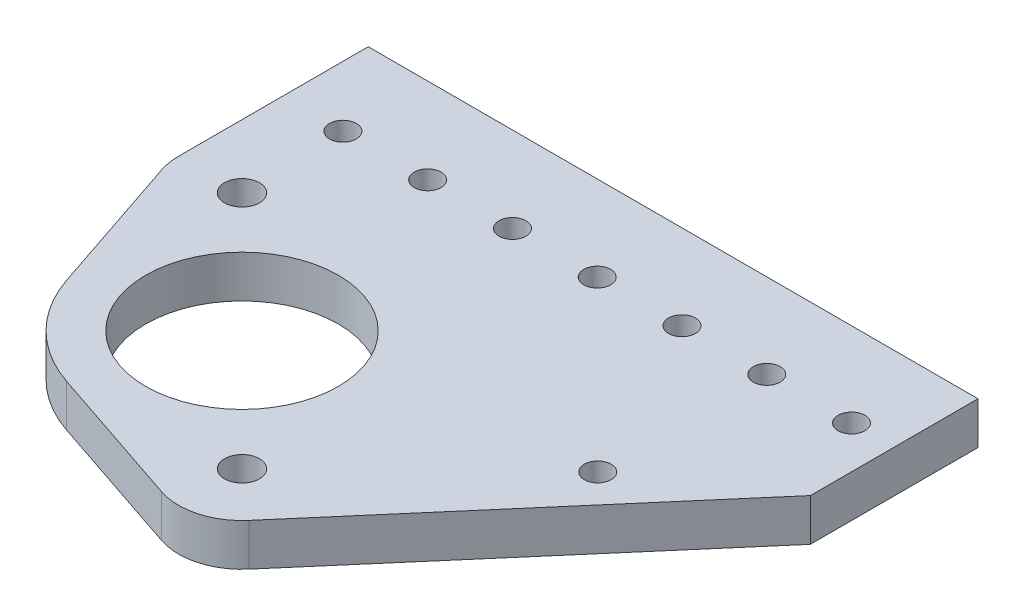
SolidWorks part; units mm, degrees
material "6061-T6 (SS)"
ref_plane "Front Plane" through (0, 0, 0) normal (0, 0, 1) x (1, 0, 0)
ref_plane "Top Plane" through (0, 0, 0) normal (0, 1, 0) x (1, 0, 0)
ref_plane "Right Plane" through (0, 0, 0) normal (1, 0, 0) x (0, 0, -1)
sketch "Sketch1" plane through (0, 0, 0) normal (0, 1, 0) x (1, 0, 0)
  line L0 (0, 0) -> (133.35, 0) construction
  line L1 (-146.05, -171.45) -> (146.05, -171.45) construction
  line L2 (-146.05, -171.45) -> (-146.05, 171.45) construction
  line L3 (-146.05, 171.45) -> (146.05, 171.45) construction
  line L4 (146.05, -171.45) -> (146.05, 171.45) construction
  line L5 (-133.35, 0) -> (-146.05, 0) construction
  line L6 (0, 133.35) -> (0, 171.45) construction
  line L7 (0, -133.35) -> (0, -171.45) construction
  line L8 (-127, 158.75) -> (-139.6999, 158.7097) construction
  line L9 (-146.05, 145.8889) -> (-225.2276, 145.8889) construction
  line L10 (0, 0) -> (-286.4034, 124.6264) construction
  line L11 (-286.4034, 124.6264) -> (-268.4429, 106.6659) construction
  line L12 (-286.4034, 124.6264) -> (-304.3639, 142.5869) construction
  line L13 (-286.4034, 124.6264) -> (-301.1697, 124.6264) construction
  line L14 (-313.8889, 171.0876) -> (-222.2495, 171.0876)
  line L15 (-313.8889, 171.0876) -> (-313.8889, 142.5869)
  line L16 (-304.3639, 142.5869) -> (-313.8889, 142.5869) construction
  line L17 (-306.1462, 117.9912) -> (-313.3926, 139.5525)
  line L18 (-293.0386, 104.8836) -> (-271.4773, 97.6372)
  line L19 (-222.2495, 145.8889) -> (-222.2495, 171.0876)
  line L20 (-261.2132, 100.4645) -> (-222.2495, 145.8889)
  line L21 (-241.2994, 158.3876) -> (-241.2994, 132.9876) construction
  circle A0 centre (0, 0) radius 133.35 construction
  circle A1 centre (-127, 158.75) radius 2.0193 construction
  circle A2 centre (-139.6999, 158.7097) radius 2.0193 construction
  circle A3 centre (-152.3999, 158.6695) radius 2.0193 construction
  circle A4 centre (-165.0998, 158.6292) radius 2.0193 construction
  circle A5 centre (-177.7997, 158.5889) radius 2.0193 construction
  circle A6 centre (-190.4997, 158.5487) radius 2.0193 construction
  circle A7 centre (-203.1996, 158.5084) radius 2.0193 construction
  circle A8 centre (-215.8996, 158.4681) radius 2.0193 construction
  circle A9 centre (-228.5995, 158.4279) radius 2.0193
  circle A10 centre (-241.2994, 158.3876) radius 2.0193
  circle A11 centre (-253.9994, 158.3473) radius 2.0193
  circle A12 centre (-266.6993, 158.3071) radius 2.0193
  circle A13 centre (-279.3992, 158.2668) radius 2.0193
  circle A14 centre (-292.0992, 158.2265) radius 2.0193
  circle A15 centre (-304.7991, 158.1863) radius 2.0193
  circle A16 centre (-317.499, 158.146) radius 2.0193 construction
  circle A17 centre (-330.199, 158.1057) radius 2.0193 construction
  circle A18 centre (-342.8989, 158.0655) radius 2.0193 construction
  circle A19 centre (-355.5989, 158.0252) radius 2.0193 construction
  circle A20 centre (-368.2988, 157.985) radius 2.0193 construction
  circle A21 centre (-380.9987, 157.9447) radius 2.0193 construction
  circle A22 centre (-393.6987, 157.9044) radius 2.0193 construction
  circle A23 centre (-286.4034, 124.6264) radius 14.478
  circle A24 centre (-268.4429, 106.6659) radius 2.6289
  circle A25 centre (-304.3639, 142.5869) radius 2.6289
  arc A27 (-293.0386, 104.8836) -> (-306.1462, 117.9912) centre (-286.4034, 124.6264) cw
  arc A28 (-313.8889, 142.5869) -> (-313.3926, 139.5525) centre (-304.3639, 142.5869) ccw
  arc A29 (-271.4773, 97.6372) -> (-261.2132, 100.4645) centre (-268.4429, 106.6659) ccw
  circle A30 centre (-241.2994, 132.9876) radius 2.0193
  dimension "D1" = 266.7
  dimension "D6" = 4.0386
  dimension "D13" = 5.2578
  dimension "D14" = 28.956
  dimension "D16" = 5.2578
  dimension "D20" = 12.7
  dimension "D21" = 9.525
  dimension "D22" = 6.35
  dimension "D23" = 6.35
  dimension "D24" = 9.525
  dimension "D26" = 4.0386
  dimension "D2" = 12.7
  dimension "D3" = 12.7
  dimension "D4" = 38.1
  dimension "D5" = 38.1
  dimension "D7" = 19.05
  dimension "D8" = 12.7
  dimension "D10" = 12.7
  dimension "D11" = 12.7
  dimension "D12" = 312.3438
  dimension "D15" = 25.4
  dimension "D17" = 25.4
  dimension "D18" = 45
  dimension "D19" = 3.302
  dimension "D25" = 25.4
  dimension "D9" = 22
extrude "Boss-Extrude1" add sketch "Sketch1" along normal blind 6.35
